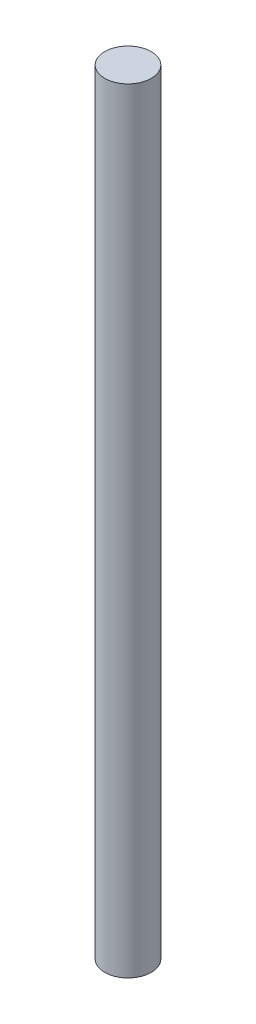
SolidWorks part; units mm, degrees
material "1060 Alloy"
ref_plane "Front Plane" through (0, 0, 0) normal (0, 0, 1) x (1, 0, 0)
ref_plane "Top Plane" through (0, 0, 0) normal (0, 1, 0) x (1, 0, 0)
ref_plane "Right Plane" through (0, 0, 0) normal (1, 0, 0) x (0, 0, -1)
sketch "Sketch1" plane through (0, 0, 0) normal (0, 1, 0) x (1, 0, 0)
  circle A0 centre (0, 0) radius 3
  dimension "D1" = 6
extrude "Boss-Extrude1" add sketch "Sketch1" along normal blind 100
